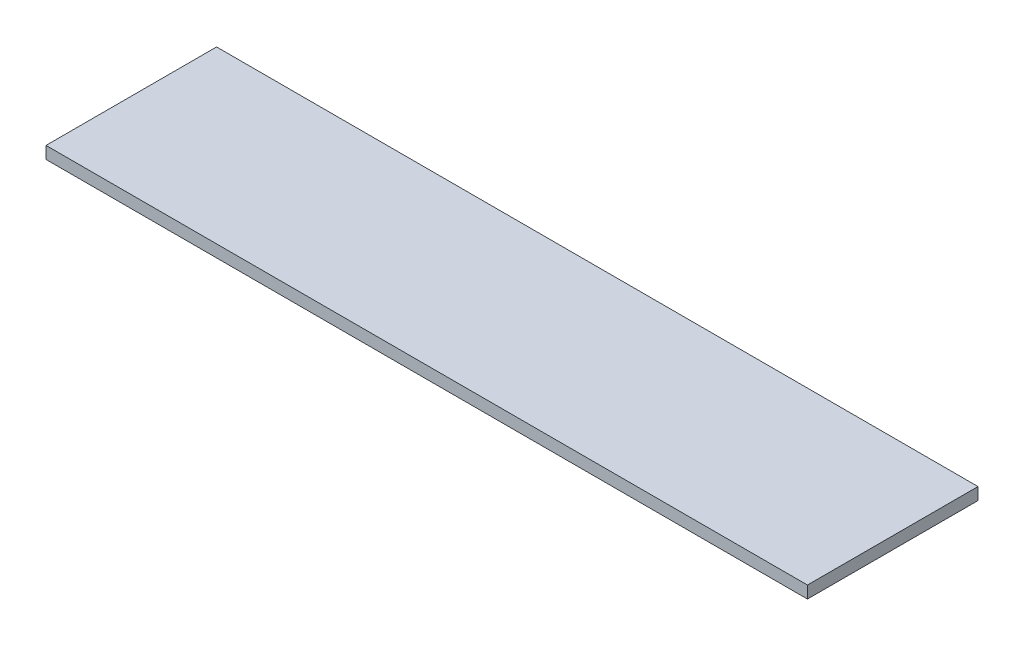
SolidWorks part; units mm, degrees
ref_plane "Front Plane" through (0, 0, 0) normal (0, 0, 1) x (1, 0, 0)
ref_plane "Top Plane" through (0, 0, 0) normal (0, 1, 0) x (1, 0, 0)
ref_plane "Right Plane" through (0, 0, 0) normal (1, 0, 0) x (0, 0, -1)
sketch "Sketch1" plane through (0, 0, 0) normal (0, 1, 0) x (1, 0, 0)
  line L1 (-25.2201, 25.3921) -> (99.7799, 25.3921)
  line L2 (-25.2201, 25.3921) -> (-25.2201, -2.6079)
  line L3 (-25.2201, -2.6079) -> (99.7799, -2.6079)
  line L4 (99.7799, 25.3921) -> (99.7799, -2.6079)
  dimension "D1" = 125
  dimension "D2" = 28
extrude "Boss-Extrude1" add sketch "Sketch1" along normal blind 2
